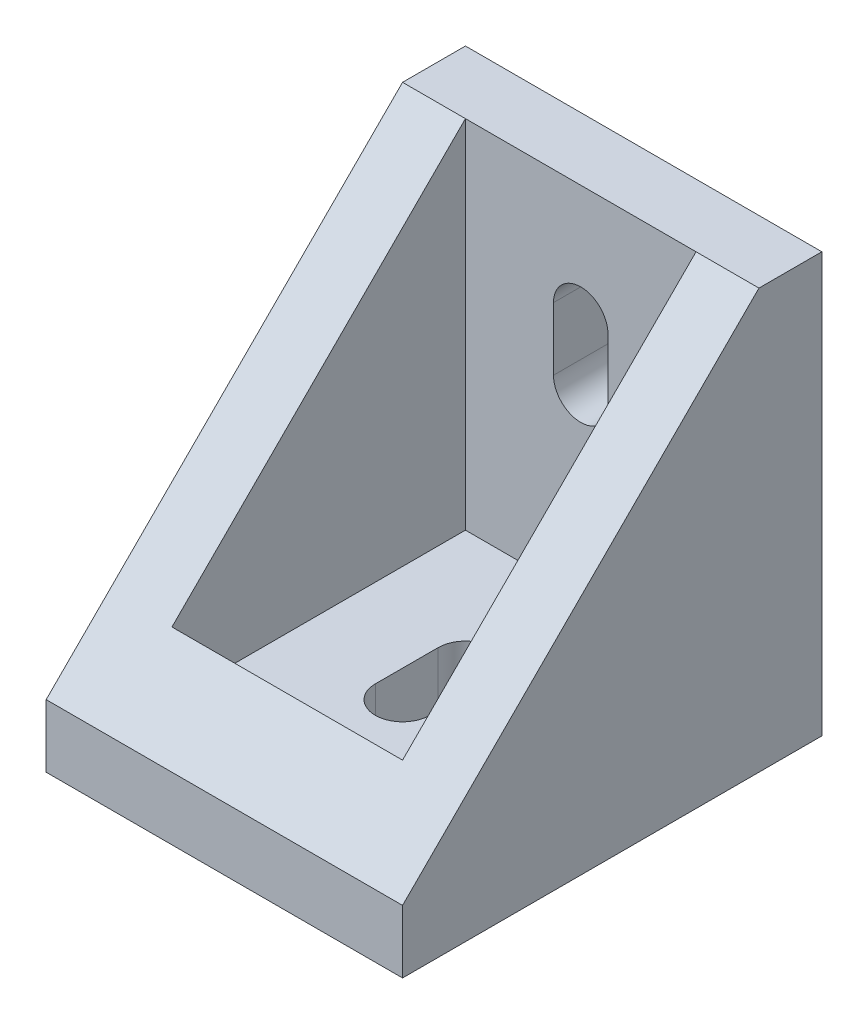
SolidWorks part; units mm, degrees
ref_plane "Front" through (0, 0, 0) normal (0, 0, 1) x (1, 0, 0)
ref_plane "Top" through (0, 0, 0) normal (0, 1, 0) x (1, 0, 0)
ref_plane "Right" through (0, 0, 0) normal (1, 0, 0) x (0, 0, -1)
sketch "Sketch1" plane through (0, 0, 0) normal (0, 1, 0) x (1, 0, 0)
  line L1 (-8.5, 10) -> (8.5, 10)
  line L2 (-8.5, 10) -> (-8.5, -10)
  line L3 (-8.5, -10) -> (8.5, -10)
  line L4 (8.5, 10) -> (8.5, -10)
  line L5 (-8.5, 10) -> (8.5, -10) construction
  line L6 (-8.5, -10) -> (8.5, 10) construction
  point P0 (0, 0)
  dimension "D1" = 17
  dimension "D2" = 20
extrude "Boss-Extrude1" add sketch "Sketch1" along normal blind 20
shell "Shell1" thickness 3
sketch "Sketch3" plane through (8.5, 0, 0) normal (1, 0, 0) x (0, 0, -1)
  line L0 (7, 20) -> (-10, 20)
  line L1 (-10, 20) -> (10, 20) construction
  line L2 (-10, 20) -> (-10, 3)
  line L3 (-10, 20) -> (-10, 0) construction
  line L4 (-10, 3) -> (7, 20)
  line L5 (-10, 0) -> (10, 0) construction
  dimension "D1" = 3
  dimension "D2" = 3
extrude "Cut-Extrude1" cut sketch "Sketch3" against normal through all
sketch "Sketch4" plane through (0, 3, 0) normal (0, 1, 0) x (1, 0, 0)
  line L0 (0, 1.5) -> (0, -1.5) construction
  line L1 (1.3, 1.5) -> (1.3, -1.5)
  line L2 (-1.3, 1.5) -> (-1.3, -1.5)
  line L5 (-4.3997, 7) -> (-4.3997, -7) construction
  line L6 (5.5, 7) -> (-5.5, 7) construction
  line L7 (-5.5, -7) -> (5.5, -7) construction
  arc A0 (1.3, 1.5) -> (-1.3, 1.5) centre (0, 1.5) ccw
  arc A1 (-1.3, -1.5) -> (1.3, -1.5) centre (0, -1.5) ccw
  point P2 (0, 0)
  point P8 (-4.3997, 0)
  point P9 (0, 0)
  dimension "D1" = 3
  dimension "D2" = 1.3
extrude "Cut-Extrude2" cut sketch "Sketch4" against normal through all
sketch "Sketch5" plane through (0, 0, -7) normal (0, 0, 1) x (1, 0, 0)
  line L0 (0, 14.5) -> (0, 11.5) construction
  line L1 (1.3, 14.5) -> (1.3, 11.5)
  line L2 (-1.3, 14.5) -> (-1.3, 11.5)
  line L3 (4.0251, 20) -> (4.0251, 6) construction
  line L4 (5.5, 20) -> (-5.5, 20) construction
  line L5 (5.5, 6) -> (-5.5, 6) construction
  arc A0 (1.3, 14.5) -> (-1.3, 14.5) centre (0, 14.5) ccw
  arc A1 (-1.3, 11.5) -> (1.3, 11.5) centre (0, 11.5) ccw
  point P3 (0, 13)
  point P14 (4.0251, 13)
  dimension "D1" = 3
  dimension "D2" = 1.3
extrude "Cut-Extrude3" cut sketch "Sketch5" against normal through all
